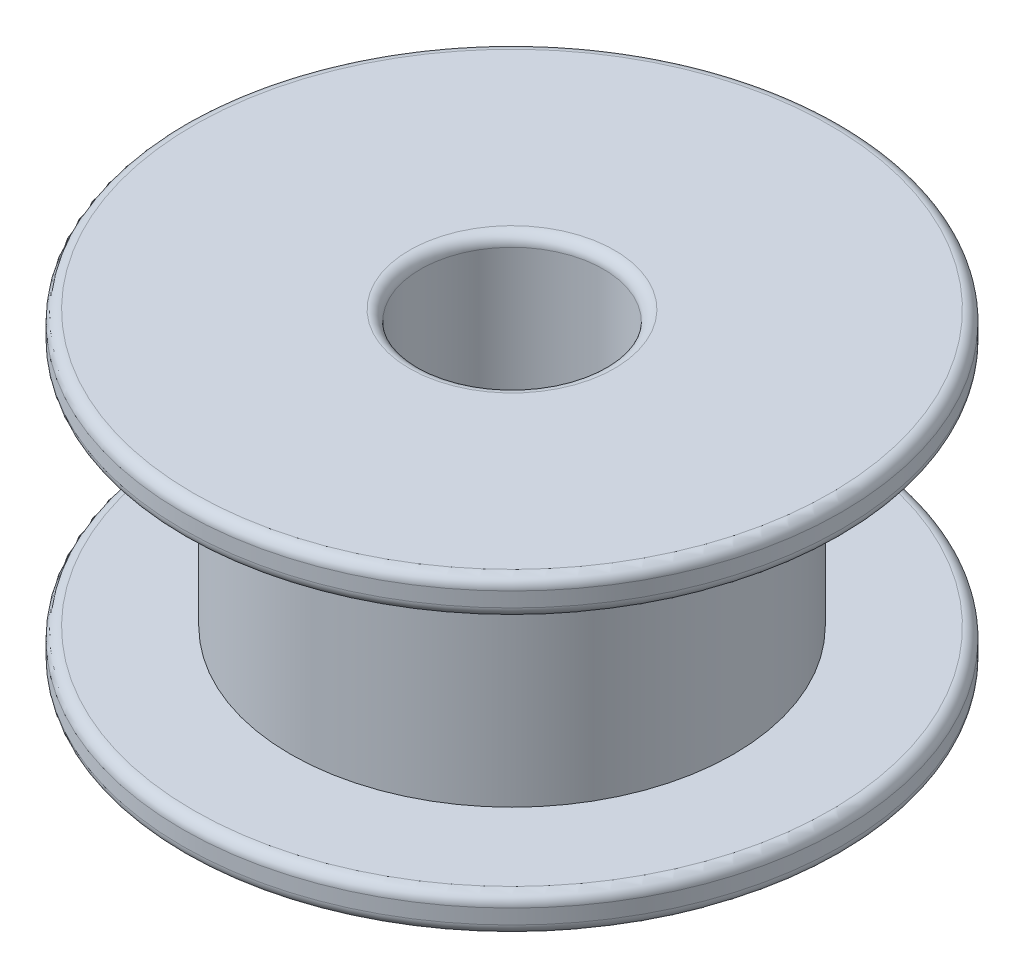
SolidWorks part; units mm, degrees
ref_plane "Front Plane" through (0, 0, 0) normal (0, 0, 1) x (1, 0, 0)
ref_plane "Top Plane" through (0, 0, 0) normal (0, 1, 0) x (1, 0, 0)
ref_plane "Right Plane" through (0, 0, 0) normal (1, 0, 0) x (0, 0, -1)
sketch "Sketch1" plane through (0, 0, 0) normal (0, 1, 0) x (1, 0, 0)
  circle A0 centre (0, 0) radius 9
  circle A1 centre (0, 0) radius 2.5
  dimension "D1" = 18
  dimension "D2" = 5
extrude "Boss-Extrude1" add sketch "Sketch1" along normal blind 1
sketch "Sketch2" plane through (0, 1, 0) normal (0, 1, 0) x (1, 0, 0)
  circle A0 centre (0, 0) radius 6.05
  circle A1 centre (0, 0) radius 2.5
  dimension "D1" = 12.1
  dimension "D2" = 5
extrude "Boss-Extrude2" add sketch "Sketch2" along normal blind 6.5
sketch "Sketch3" plane through (0, 7.5, 0) normal (0, 1, 0) x (1, 0, 0)
  circle A0 centre (0, 0) radius 9
  circle A1 centre (0, 0) radius 2.5
  dimension "D1" = 18
  dimension "D2" = 5
extrude "Boss-Extrude3" add sketch "Sketch3" along normal blind 1
fillet "Fillet1" radius 0.3 6 edges at (0, 0, 2.5) (0, 0, 9) (0, 8.5, 2.5) (0, 8.5, 9) (0, 7.5, 9) (0, 1, 9)
